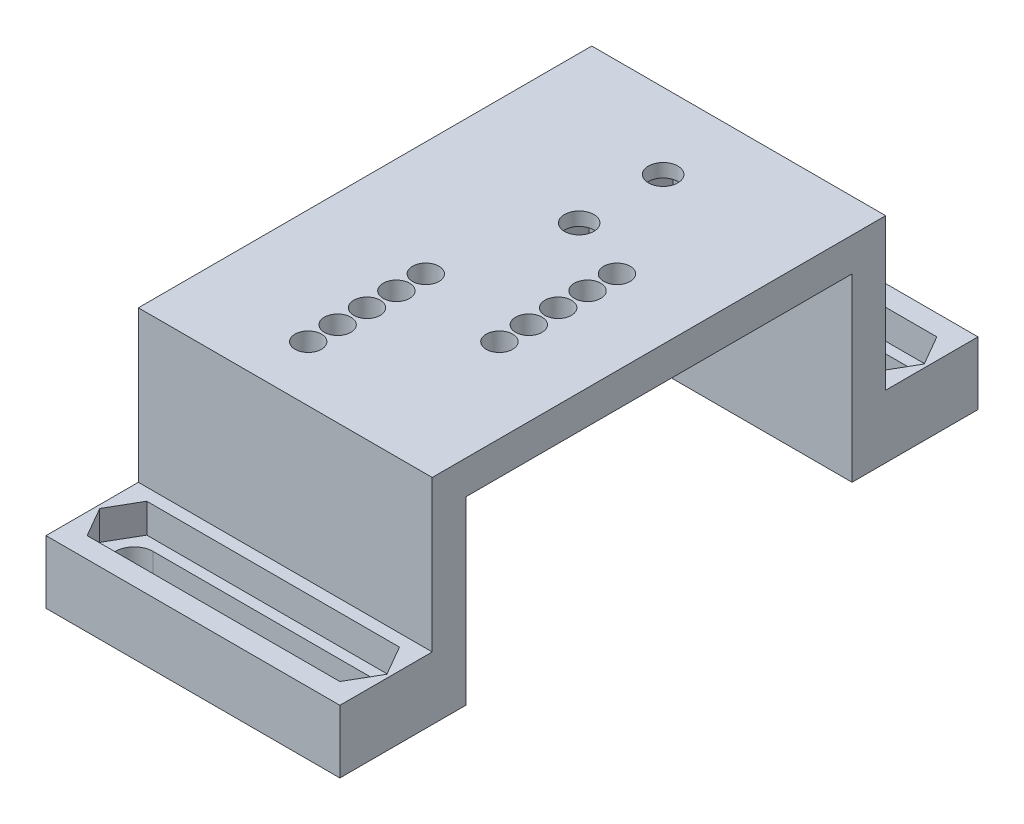
SolidWorks part; units mm, degrees
ref_plane "Alzado" through (0, 0, 0) normal (0, 0, 1) x (1, 0, 0)
ref_plane "Planta" through (0, 0, 0) normal (0, 1, 0) x (1, 0, 0)
ref_plane "Vista lateral" through (0, 0, 0) normal (1, 0, 0) x (0, 0, -1)
sketch "Croquis1" plane through (0, 0, 0) normal (1, 0, 0) x (0, 0, -1)
  line L0 (-38, -18) -> (-27, -18)
  line L1 (-27, -18) -> (-27, 0)
  line L2 (-27, 0) -> (27, 0)
  line L3 (27, 0) -> (27, -18)
  line L4 (27, -18) -> (38, -18)
  line L5 (-38, -25.5) -> (-23, -25.5)
  line L6 (-23, -25.5) -> (-23, -4)
  line L7 (-23, -4) -> (23, -4)
  line L8 (23, -4) -> (23, -25.5)
  line L9 (23, -25.5) -> (38, -25.5)
  line L10 (-38, -18) -> (-38, -25.5)
  line L11 (38, -18) -> (38, -25.5)
  dimension "D1" = 54
  dimension "D2" = 76
  dimension "D4" = 25.5
  dimension "D3" = 4
  dimension "D5" = 4
  dimension "D6" = 4
  dimension "D7" = 7.5
extrude "Saliente-Extruir1" add sketch "Croquis1" along normal blind 35
sketch "Croquis2" plane through (0, -18, 0) normal (0, 1, 0) x (1, 0, 0)
  line L0 (4.5, 32) -> (30.5, 32) construction
  line L1 (4.5, 34.25) -> (30.5, 34.25)
  line L2 (4.5, 29.75) -> (30.5, 29.75)
  line L3 (4.5, -32) -> (30.5, -32) construction
  line L4 (4.5, -29.75) -> (30.5, -29.75)
  line L5 (4.5, -34.25) -> (30.5, -34.25)
  line L6 (17.5, 32) -> (17.5, 38) construction
  line L7 (35, 38) -> (0, 38) construction
  line L8 (17.5, -32) -> (17.5, -38) construction
  line L9 (35, -38) -> (0, -38) construction
  arc A0 (4.5, 34.25) -> (4.5, 29.75) centre (4.5, 32) ccw
  arc A1 (30.5, 29.75) -> (30.5, 34.25) centre (30.5, 32) ccw
  arc A2 (4.5, -29.75) -> (4.5, -34.25) centre (4.5, -32) ccw
  arc A3 (30.5, -34.25) -> (30.5, -29.75) centre (30.5, -32) ccw
  point P2 (17.5, 32)
  point P7 (17.5, -32)
  dimension "D2" = 2.25
  dimension "D1" = 64
  dimension "D3" = 26
extrude "Cortar-Extruir1" cut sketch "Croquis2" against normal through all
sketch "Croquis3" plane through (0, 0, 0) normal (0, 1, 0) x (1, 0, 0)
  line L0 (17.5, 27) -> (17.5, -27) construction
  line L1 (17.5, 0) -> (35, 0) construction
  line L2 (35, 27) -> (35, -27) construction
  line L3 (35, 27) -> (0, 27) construction
  line L4 (35, -27) -> (0, -27) construction
  line L6 (17.5, 0) -> (0, 0) construction
  line L7 (0, 27) -> (0, -27) construction
  circle A0 centre (17.5, 18) radius 1.75
  circle A1 centre (17.5, 8) radius 1.75
  dimension "D1" = 3.5
  dimension "D3" = 10
  dimension "D2" = 9
extrude "Cortar-Extruir2" cut sketch "Croquis3" against normal through all
sketch "Croquis4" plane through (0, -4, 0) normal (0, -1, 0) x (1, 0, 0)
  line L1 (20.6754, -8) -> (19.0877, -5.25)
  line L2 (19.0877, -5.25) -> (15.9123, -5.25)
  line L3 (15.9123, -5.25) -> (14.3246, -8)
  line L4 (14.3246, -8) -> (15.9123, -10.75)
  line L5 (15.9123, -10.75) -> (19.0877, -10.75)
  line L6 (19.0877, -10.75) -> (20.6754, -8)
  line L7 (20.6754, -18) -> (19.0877, -15.25)
  line L8 (19.0877, -15.25) -> (15.9123, -15.25)
  line L9 (15.9123, -15.25) -> (14.3246, -18)
  line L10 (14.3246, -18) -> (15.9123, -20.75)
  line L11 (15.9123, -20.75) -> (19.0877, -20.75)
  line L12 (19.0877, -20.75) -> (20.6754, -18)
  circle A0 centre (17.5, -8) radius 2.75 construction
  circle A1 centre (17.5, -18) radius 2.75 construction
  dimension "D1" = 5.5
extrude "Cortar-Extruir3" cut sketch "Croquis4" against normal blind 2.4
sketch "Croquis5" plane through (0, -18, 0) normal (0, -1, 0) x (1, 0, 0)
  line L0 (0.4008, -32) -> (2.4504, -28.45)
  line L1 (8.5992, -32) -> (6.5496, -28.45) construction
  line L2 (6.5496, -28.45) -> (2.4504, -28.45) construction
  line L3 (2.4504, -28.45) -> (0.4008, -32) construction
  line L4 (0.4008, -32) -> (2.4504, -35.55) construction
  line L5 (2.4504, -35.55) -> (6.5496, -35.55) construction
  line L6 (6.5496, -35.55) -> (8.5992, -32) construction
  line L7 (26.4008, -32) -> (28.4504, -35.55) construction
  line L8 (28.4504, -35.55) -> (32.5496, -35.55) construction
  line L9 (32.5496, -35.55) -> (34.5992, -32) construction
  line L10 (34.5992, -32) -> (32.5496, -28.45) construction
  line L11 (32.5496, -28.45) -> (28.4504, -28.45) construction
  line L12 (28.4504, -28.45) -> (26.4008, -32) construction
  line L13 (2.4504, -28.45) -> (32.5496, -28.45)
  line L14 (32.5496, -28.45) -> (34.5992, -32)
  line L15 (34.5992, -32) -> (32.5496, -35.55)
  line L16 (32.5496, -35.55) -> (2.4504, -35.55)
  line L17 (2.4504, -35.55) -> (0.4008, -32)
  line L18 (35, 0) -> (17.7277, 0) construction
  line L19 (35, 23) -> (35, -23) construction
  line L20 (0.4008, 32) -> (2.4504, 28.45)
  line L21 (2.4504, 35.55) -> (0.4008, 32)
  line L22 (32.5496, 35.55) -> (2.4504, 35.55)
  line L23 (34.5992, 32) -> (32.5496, 35.55)
  line L24 (32.5496, 28.45) -> (34.5992, 32)
  line L25 (2.4504, 28.45) -> (32.5496, 28.45)
  circle A0 centre (4.5, -32) radius 3.55 construction
  circle A1 centre (30.5, -32) radius 3.55 construction
  dimension "D1" = 7.1
extrude "Cortar-Extruir4" cut sketch "Croquis5" along normal blind 3.5
sketch "Croquis8" plane through (0, -4, 0) normal (0, -1, 0) x (1, 0, 0)
  line L0 (25, 9) -> (25, 20.3844) construction
  line L1 (25, 20.3844) -> (13.6156, 20.3844) construction
  line L2 (17.5, -8) -> (17.5, -42.9447) construction
  line L3 (25, 9) -> (16.2006, 9) construction
  line L5 (17.5, -8) -> (15.605, -8) construction
  circle A0 centre (25, 9) radius 1.575
  circle A1 centre (13.6156, 20.3844) radius 1.575
  circle A2 centre (13.6156, 16.8844) radius 1.575
  circle A3 centre (25, 5.5) radius 1.575
  circle A4 centre (13.6156, 13.3844) radius 1.575
  circle A5 centre (25, 2) radius 1.575
  circle A6 centre (13.6156, 9.8844) radius 1.575
  circle A7 centre (25, -1.5) radius 1.575
  circle A8 centre (13.6156, 6.3844) radius 1.575
  circle A9 centre (25, -5) radius 1.575
  dimension "D3" = 3.15
  dimension "D1" = 11.3844
  dimension "D2" = 11.3844
  dimension "D4" = 7.5
  dimension "D5" = 17
  dimension "D7" = 3.5
  dimension "D6" = 5
extrude "Cortar-Extruir6" cut sketch "Croquis8" against normal through all
sketch "Croquis9" plane through (0, -4, 0) normal (0, -1, 0) x (1, 0, 0)
  line L1 (16.791, 20.3844) -> (15.2033, 23.1344)
  line L2 (15.2033, 23.1344) -> (12.0279, 23.1344)
  line L3 (12.0279, 23.1344) -> (10.4402, 20.3844)
  line L4 (10.4402, 20.3844) -> (12.0279, 17.6344)
  line L5 (12.0279, 17.6344) -> (15.2033, 17.6344)
  line L6 (15.2033, 17.6344) -> (16.791, 20.3844)
  circle A0 centre (13.6156, 20.3844) radius 2.75 construction
  dimension "D1" = 5.5
